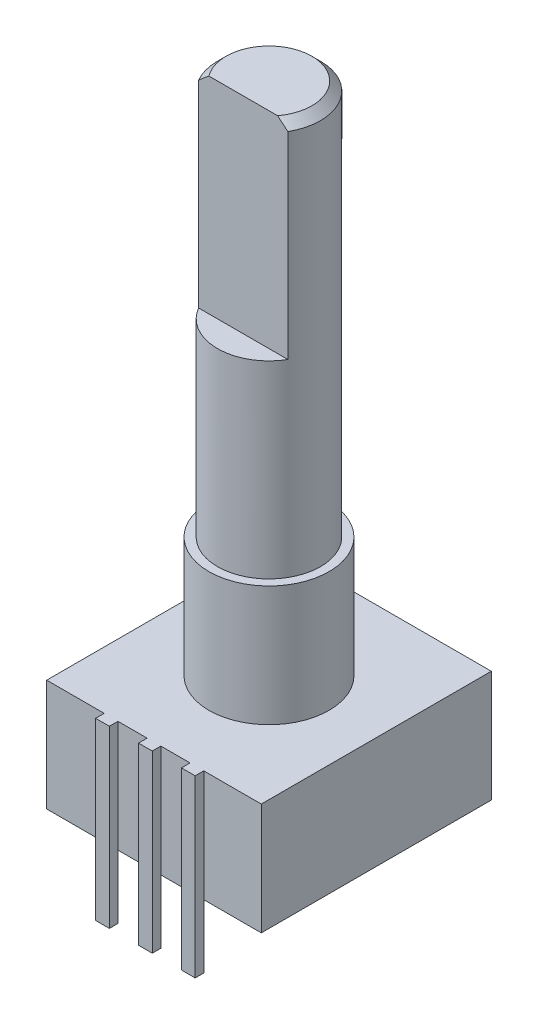
SolidWorks part; units mm, degrees
ref_plane "Front Plane" through (0, 0, 0) normal (0, 0, 1) x (1, 0, 0)
ref_plane "Top Plane" through (0, 0, 0) normal (0, 1, 0) x (1, 0, 0)
ref_plane "Right Plane" through (0, 0, 0) normal (1, 0, 0) x (0, 0, -1)
sketch "Sketch1" plane through (0, 0, 0) normal (0, 1, 0) x (1, 0, 0)
  line L1 (6.25, -6.7) -> (-6.25, -6.7)
  line L2 (6.25, -6.7) -> (6.25, 6.7)
  line L3 (6.25, 6.7) -> (-6.25, 6.7)
  line L4 (-6.25, -6.7) -> (-6.25, 6.7)
  line L5 (0, 6.7) -> (0, -6.7) construction
  line L6 (6.25, 0) -> (-6.25, 0) construction
  point P0 (0, 0)
  dimension "D1" = 12.5
  dimension "D2" = 13.4
extrude "Boss-Extrude1" add sketch "Sketch1" against normal blind 6.5
sketch "Sketch2" plane through (0, 0, 0) normal (0, 1, 0) x (1, 0, 0)
  circle A0 centre (0, 0) radius 3.5
  dimension "D1" = 7
extrude "Boss-Extrude2" add sketch "Sketch2" along normal blind 7
cosmetic thread "Cosmetic Thread1" parameters "D1"=5, "D2"=5.891
sketch "Sketch3" plane through (0, 7, 0) normal (0, 1, 0) x (1, 0, 0)
  circle A0 centre (0, 0) radius 3
  dimension "D1" = 6
extrude "Boss-Extrude3" add sketch "Sketch3" along normal blind 23
chamfer "Chamfer1" distance 0.5 angle 45 1 edges at (0, 30, 3)
sketch "Sketch4" plane through (0, 30, 0) normal (0, 1, 0) x (1, 0, 0)
  line L0 (-2.5981, -1.5) -> (2.5981, -1.5)
  circle A0 centre (0, 0) radius 3 construction
  circle A1 centre (0, 0) radius 3 construction
  arc A2 (-2.5981, -1.5) -> (2.5981, -1.5) centre (0, 0) ccw
  point P4 (0, 3)
  dimension "D1" = 4.5
extrude "Cut-Extrude1" cut sketch "Sketch4" against normal blind 12
sketch "Sketch5" plane through (0, 0, 6.7) normal (0, 0, 1) x (1, 0, 0)
  line L0 (0, 0) -> (0, -10.2) construction
  line L1 (-2.5, 0) -> (-2.5, -10.2) construction
  line L2 (-6.25, 0) -> (6.25, 0) construction
  line L3 (-2.9, 0) -> (-2.9, -10.2)
  line L4 (2.5, 0) -> (2.5, -10.2) construction
  line L5 (-0.4, 0) -> (-0.4, -10.2)
  line L6 (2.1, 0) -> (2.1, -10.2)
  line L7 (-2.1, 0) -> (-2.1, -10.2)
  line L8 (0.4, 0) -> (0.4, -10.2)
  line L9 (2.9, 0) -> (2.9, -10.2)
  line L10 (-2.9, 0) -> (-2.1, 0)
  line L11 (-2.9, -10.2) -> (-2.1, -10.2)
  line L12 (-0.4, 0) -> (0.4, 0)
  line L13 (-0.4, -10.2) -> (0.4, -10.2)
  line L14 (2.1, 0) -> (2.9, 0)
  line L15 (2.1, -10.2) -> (2.9, -10.2)
  line L16 (-6.25, -6.5) -> (6.25, -6.5) construction
  dimension "D1" = 5
  dimension "D2" = 2.5
  dimension "D5" = 3.7
  dimension "D3" = 0.4
  dimension "D4" = 0.4
extrude "Boss-Extrude4" add sketch "Sketch5" along normal blind 0.5
